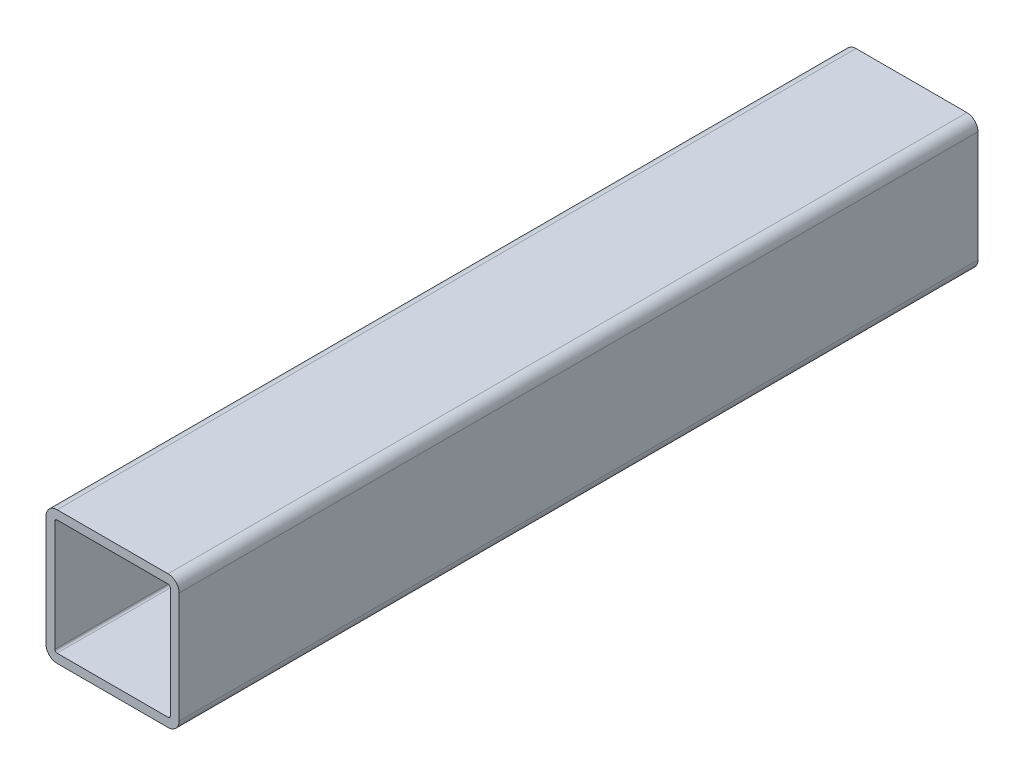
SolidWorks part; units mm, degrees
ref_plane "Front Plane" through (0, 0, 0) normal (0, 0, 1) x (1, 0, 0)
ref_plane "Top Plane" through (0, 0, 0) normal (0, 1, 0) x (1, 0, 0)
ref_plane "Right Plane" through (0, 0, 0) normal (1, 0, 0) x (0, 0, -1)
sketch "Sketch1" plane through (0, 0, 0) normal (0, 0, 1) x (1, 0, 0)
  line L1 (-15.875, 19.05) -> (15.875, 19.05)
  line L2 (-19.05, 15.875) -> (-19.05, -15.875)
  line L3 (-15.875, -19.05) -> (15.875, -19.05)
  line L4 (19.05, 15.875) -> (19.05, -15.875)
  line L5 (-19.05, 19.05) -> (19.05, -19.05) construction
  line L6 (-19.05, -19.05) -> (19.05, 19.05) construction
  arc A0 (-19.05, -15.875) -> (-15.875, -19.05) centre (-15.875, -15.875) ccw
  arc A1 (15.875, -19.05) -> (19.05, -15.875) centre (15.875, -15.875) ccw
  arc A2 (19.05, 15.875) -> (15.875, 19.05) centre (15.875, 15.875) ccw
  arc A3 (-15.875, 19.05) -> (-19.05, 15.875) centre (-15.875, 15.875) ccw
  point P0 (0, 0)
  dimension "D3" = 3.175
  dimension "D1" = 38.1
  dimension "D2" = 38.1
extrude "Extrude-Thin1" add sketch "Sketch1" along normal mid plane 228.6 thin
sketch "Sketch7" plane through (0, 0, 114.3) normal (0, 0, 1) x (1, 0, 0)
  line L0 (16.51, 0) -> (-16.51, 0) construction
  line L1 (16.51, -15.875) -> (16.51, 15.875) construction
  line L2 (-16.51, 15.875) -> (-16.51, -15.875) construction
  line L3 (0, 16.51) -> (0, -16.51) construction
  line L4 (15.875, 16.51) -> (-15.875, 16.51) construction
  line L5 (-15.875, -16.51) -> (15.875, -16.51) construction
sketch "Sketch9" plane through (0, 0, -114.3) normal (0, 0, -1) x (-1, 0, 0)
  line L0 (0, 16.51) -> (0, -16.51) construction
  line L1 (-15.875, 16.51) -> (15.875, 16.51) construction
  line L2 (15.875, -16.51) -> (-15.875, -16.51) construction
  line L3 (16.51, 0) -> (-16.51, 0) construction
  line L4 (16.51, 15.875) -> (16.51, -15.875) construction
  line L5 (-16.51, -15.875) -> (-16.51, 15.875) construction
